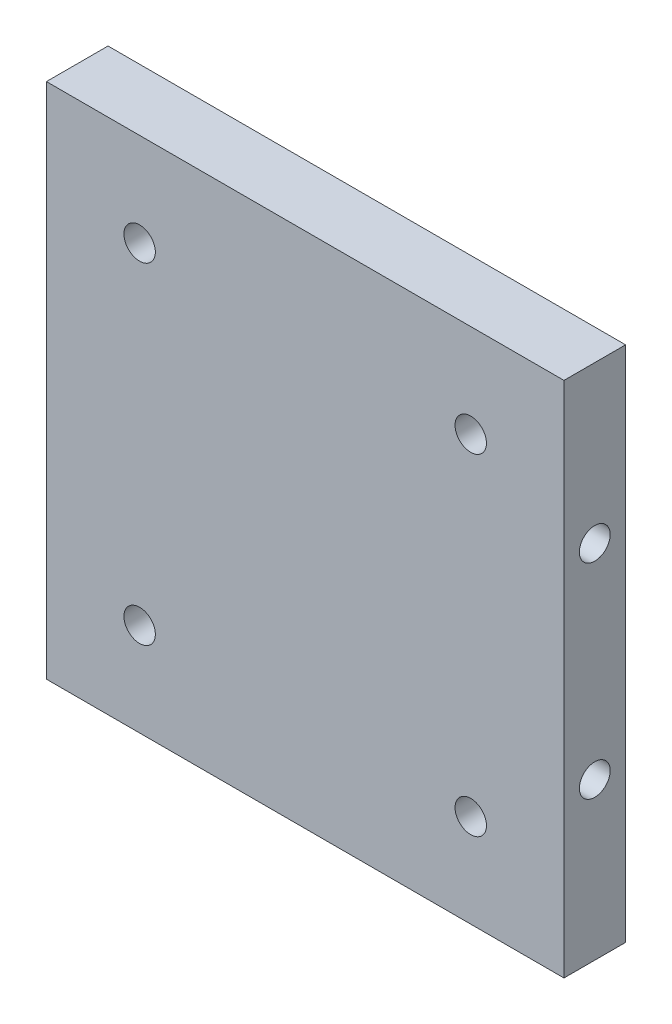
SolidWorks part; units mm, degrees
material "6063-T5"
ref_plane "前视基准面" through (0, 0, 0) normal (0, 0, 1) x (1, 0, 0)
ref_plane "上视基准面" through (0, 0, 0) normal (0, 1, 0) x (1, 0, 0)
ref_plane "右视基准面" through (0, 0, 0) normal (1, 0, 0) x (0, 0, -1)
other "Configuration Table"
sketch "草图1" plane through (0, 0, 0) normal (0, 0, 1) x (1, 0, 0)
  line L1 (-21, -21) -> (21, -21)
  line L2 (-21, -21) -> (-21, 21)
  line L3 (-21, 21) -> (21, 21)
  line L4 (21, -21) -> (21, 21)
  line L5 (-21, -21) -> (21, 21) construction
  line L6 (-21, 21) -> (21, -21) construction
  point P0 (0, 0)
  dimension "D1" = 42
  dimension "D2" = 42
extrude "凸台-拉伸1" add sketch "草图1" along normal blind 5
sketch "草图2" plane through (0, 0, 5) normal (0, 0, 1) x (1, 0, 0)
  line L0 (13.435, 13.435) -> (0, 0) construction
  line L1 (0, 0) -> (19, 0) construction
  circle A0 centre (0, 0) radius 19 construction
  circle A1 centre (13.435, 13.435) radius 1.275
  circle A2 centre (13.435, -13.435) radius 1.275
  circle A3 centre (-13.435, -13.435) radius 1.275
  circle A4 centre (-13.435, 13.435) radius 1.275
  point P16 (0, 0)
  dimension "D1" = 38
  dimension "D3" = 2.55
  dimension "D2" = 45
  dimension "D4" = 4
extrude "切除-拉伸1" cut sketch "草图2" against normal through all
hole_wizard "M3 螺纹孔1" positions "草图3" profile "草图4" tap size "M3" standard "GB" end condition through all
sketch "草图3" plane through (21, 0, 0) normal (1, 0, 0) x (0, 0, -1)
  line L0 (-2.5, 8.3) -> (-2.5, 21) construction
  line L1 (-5, 21) -> (0, 21) construction
  point P0 (-2.5, 8.3)
  dimension "D1" = 12.7
sketch "草图4" plane through (21, 8.3, 2.5) normal (0, 1, 0) x (0, 0, -1)
  line L0 (0, 0) -> (0, 42)
  line L1 (0, 42) -> (1.25, 42)
  line L2 (1.25, 42) -> (1.25, 0)
  line L5 (1.25, 0) -> (0, 0)
  line L11 (0, -6.35) -> (0, 107.95) construction
  dimension "通孔螺纹孔钻头直径" = 2.5
  dimension "通孔螺纹孔钻头深度" = 42
cosmetic thread "孔螺蚊线1"
mirror "镜向1" about plane through (0, 0, 0) normal (0, 1, 0) of "M3 螺纹孔1"
